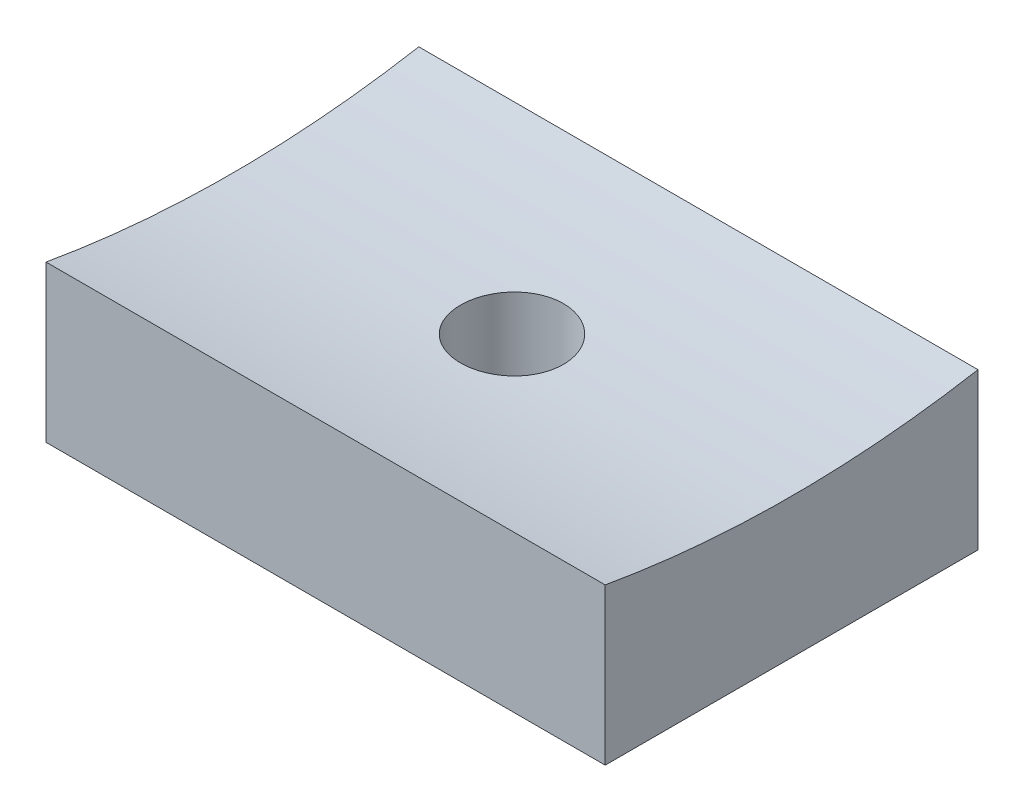
SolidWorks part; units mm, degrees
material "6061 Alloy"
ref_plane "Front Plane" through (0, 0, 0) normal (0, 0, 1) x (1, 0, 0)
ref_plane "Top Plane" through (0, 0, 0) normal (0, 1, 0) x (1, 0, 0)
ref_plane "Right Plane" through (0, 0, 0) normal (1, 0, 0) x (0, 0, -1)
sketch "Sketch1" plane through (0, 0, 0) normal (0, 1, 0) x (1, 0, 0)
  line L1 (-9.525, 6.35) -> (9.525, 6.35)
  line L2 (-9.525, 6.35) -> (-9.525, -6.35)
  line L3 (-9.525, -6.35) -> (9.525, -6.35)
  line L4 (9.525, 6.35) -> (9.525, -6.35)
  dimension "D1" = 12.7
  dimension "D2" = 19.05
  dimension "D3" = 9.525
  dimension "D4" = 6.35
extrude "Extrude1" add sketch "Sketch1" along normal blind 41.275
sketch "Sketch2" plane through (-9.525, 0, 0) normal (-1, 0, 0) x (0, 0, 1)
  line L0 (-6.35, 41.275) -> (6.35, 41.275) construction
  circle A0 centre (0, 41.275) radius 36.5125
extrude "Cut-Extrude1" cut sketch "Sketch2" against normal blind 41.275
hole_wizard "#6-32 Tapped Hole1" positions "3DSketch1" profile "Sketch3" tap size "#6-32" standard "Ansi Inch"
sketch3d "3DSketch1"
  line L0 (-9.525, 0, -6.35) -> (-9.525, 0, 6.35) construction
  line L1 (-9.525, 0, 6.35) -> (9.525, 0, 6.35) construction
  point P0 (0, 0, 0)
  point P3 (0, 0, 0)
  dimension "D1" = 9.525
  dimension "D2" = 6.35
sketch "Sketch3" plane through (0, 0, 0) normal (1, 0, 0) x (0, 0, -1)
  line L0 (0, 0) -> (0, 10.2107)
  line L1 (0, 10.2107) -> (1.3525, 9.398)
  line L2 (1.3525, 9.398) -> (1.3525, 7.112)
  line L3 (1.3525, 7.112) -> (1.7526, 7.112)
  line L4 (1.7526, 7.112) -> (1.7526, 0)
  line L5 (1.7526, 0) -> (0, 0)
  line L10 (0, 10.2107) -> (-1.3526, 9.398) construction
  line L11 (0, -6.35) -> (0, 107.95) construction
  dimension "Tap Drill Dia." = 2.7051
  dimension "Tap Drill Depth" = 9.398
  dimension "Thread Major Dia." = 3.5052
  dimension "Thread Depth" = 7.112
  dimension "Drill Angle" = 118
